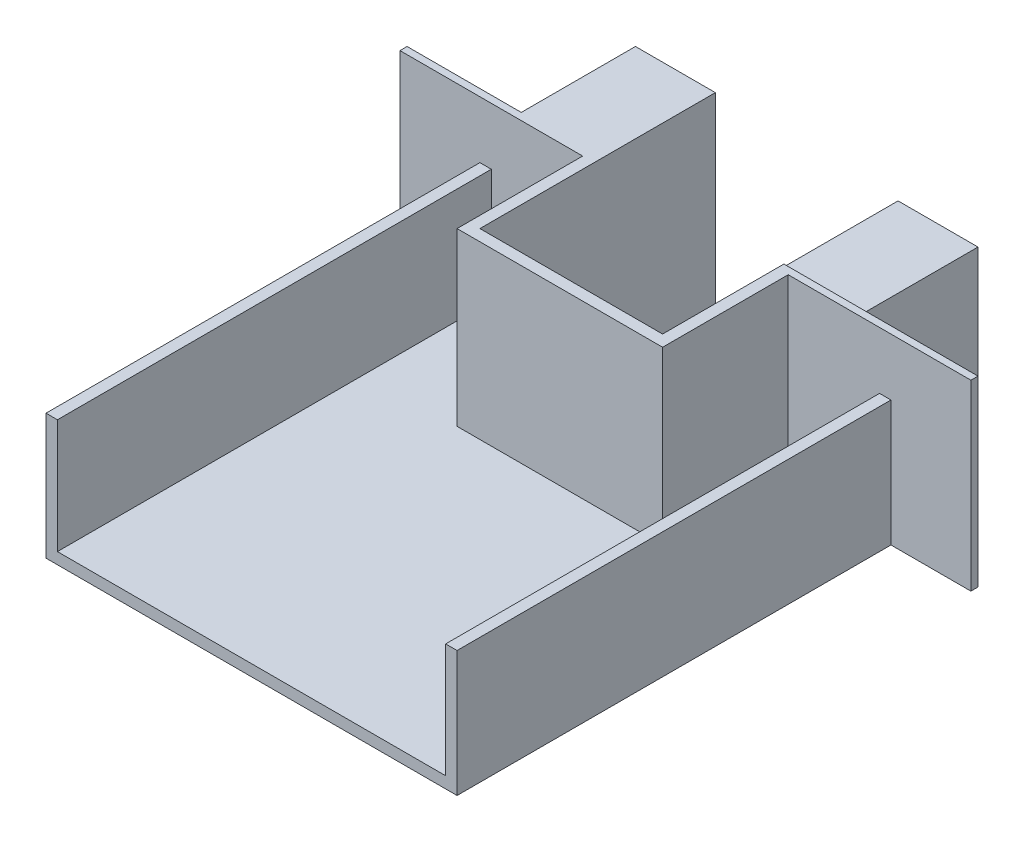
SolidWorks part; units mm, degrees
ref_plane "Front Plane" through (0, 0, 0) normal (0, 0, 1) x (1, 0, 0)
ref_plane "Top Plane" through (0, 0, 0) normal (0, 1, 0) x (1, 0, 0)
ref_plane "Right Plane" through (0, 0, 0) normal (1, 0, 0) x (0, 0, -1)
sketch "Sketch2" plane through (0, 0, 0) normal (0, 1, 0) x (1, 0, 0)
  line L1 (-90, 95) -> (90, 95)
  line L2 (-90, 95) -> (-90, -95)
  line L3 (-90, -95) -> (90, -95)
  line L4 (90, 95) -> (90, -95)
  line L5 (-90, 95) -> (90, -95) construction
  line L6 (-90, -95) -> (90, 95) construction
  point P0 (0, 0)
  dimension "D1" = 180
  dimension "D2" = 190
extrude "Boss-Extrude3" add sketch "Sketch2" along normal blind 5
sketch "Sketch4" plane through (0, 5, 0) normal (0, 1, 0) x (1, 0, 0)
  line L0 (-90, -95) -> (90, -95) construction
  line L3 (-90, 95) -> (-85, 95)
  line L4 (-90, 95) -> (-90, -95)
  line L5 (-90, -95) -> (-85, -95)
  line L6 (-85, 95) -> (-85, -95)
  line L8 (90, 95) -> (85, 95)
  line L9 (90, 95) -> (90, -95)
  line L10 (90, -95) -> (85, -95)
  line L11 (85, 95) -> (85, -95)
  dimension "D1" = 5
  dimension "D2" = 5
extrude "Boss-Extrude4" add sketch "Sketch4" along normal blind 50
sketch "Sketch6" plane through (0, 0, 0) normal (0, 1, 0) x (1, 0, 0)
  line L0 (90, -95) -> (90, 95) construction
  line L1 (-125, 95) -> (125, 95)
  line L2 (-125, 95) -> (-125, 98.109)
  line L3 (-125, 98.109) -> (125, 98.109)
  line L4 (125, 95) -> (125, 98.109)
  dimension "D1" = 250
  dimension "D2" = 35
extrude "Boss-Extrude6" add sketch "Sketch6" along normal blind 80
sketch "Sketch7" plane through (0, 0, -98.109) normal (0, 0, -1) x (-1, 0, 0)
  line L0 (99, 0) -> (-99, 0) construction
  line L1 (-75, 78.9484) -> (-40, 78.9484)
  line L2 (-75, 78.9484) -> (-75, 0)
  line L3 (-75, 0) -> (-40, 0)
  line L4 (-40, 78.9484) -> (-40, 0)
  line L5 (-125, 80) -> (125, 80) construction
  line L6 (40, 80) -> (75, 80)
  line L7 (40, 80) -> (40, 0)
  line L8 (40, 0) -> (75, 0)
  line L9 (75, 80) -> (75, 0)
  line L10 (-125, 80) -> (-125, 0) construction
  line L11 (125, 80) -> (125, 0) construction
  dimension "D1" = 80
  dimension "D2" = 50
  dimension "D3" = 50
  dimension "D4" = 35
extrude "Boss-Extrude7" add sketch "Sketch7" along normal blind 50
sketch "Sketch8" plane through (0, 80, 0) normal (0, 1, 0) x (1, 0, 0)
  line L0 (-125, 95) -> (125, 95) construction
  line L1 (-40, 98.109) -> (40, 98.109)
  line L2 (-40, 98.109) -> (-40, 95)
  line L3 (-40, 95) -> (40, 95)
  line L4 (40, 98.109) -> (40, 95)
extrude "Cut-Extrude1" cut sketch "Sketch8" against normal blind 123
sketch "Sketch9" plane through (0, 5, 0) normal (0, 1, 0) x (1, 0, 0)
  line L1 (-40, 95) -> (40, 95)
  line L2 (-40, 95) -> (-40, 45)
  line L3 (-40, 45) -> (40, 45)
  line L4 (40, 95) -> (40, 45)
  dimension "D1" = 50
extrude "Cut-Extrude2" cut sketch "Sketch9" against normal blind 123
sketch "Sketch10" plane through (0, 5, 0) normal (0, 1, 0) x (1, 0, 0)
  line L0 (-40, 95) -> (-40, 45)
  line L1 (-40, 45) -> (40, 45)
  line L2 (40, 45) -> (40, 95)
  line L3 (40, 95) -> (45, 95)
  line L4 (85, 95) -> (40, 95) construction
  line L5 (45, 95) -> (45, 40)
  line L6 (45, 40) -> (-45, 40)
  line L7 (-45, 40) -> (-45, 95)
  line L8 (-125, 95) -> (-40, 95) construction
  line L9 (-45, 95) -> (-40, 95)
  dimension "D1" = 5
  dimension "D2" = 5
  dimension "D3" = 5
extrude "Boss-Extrude8" add sketch "Sketch10" along normal blind 75
